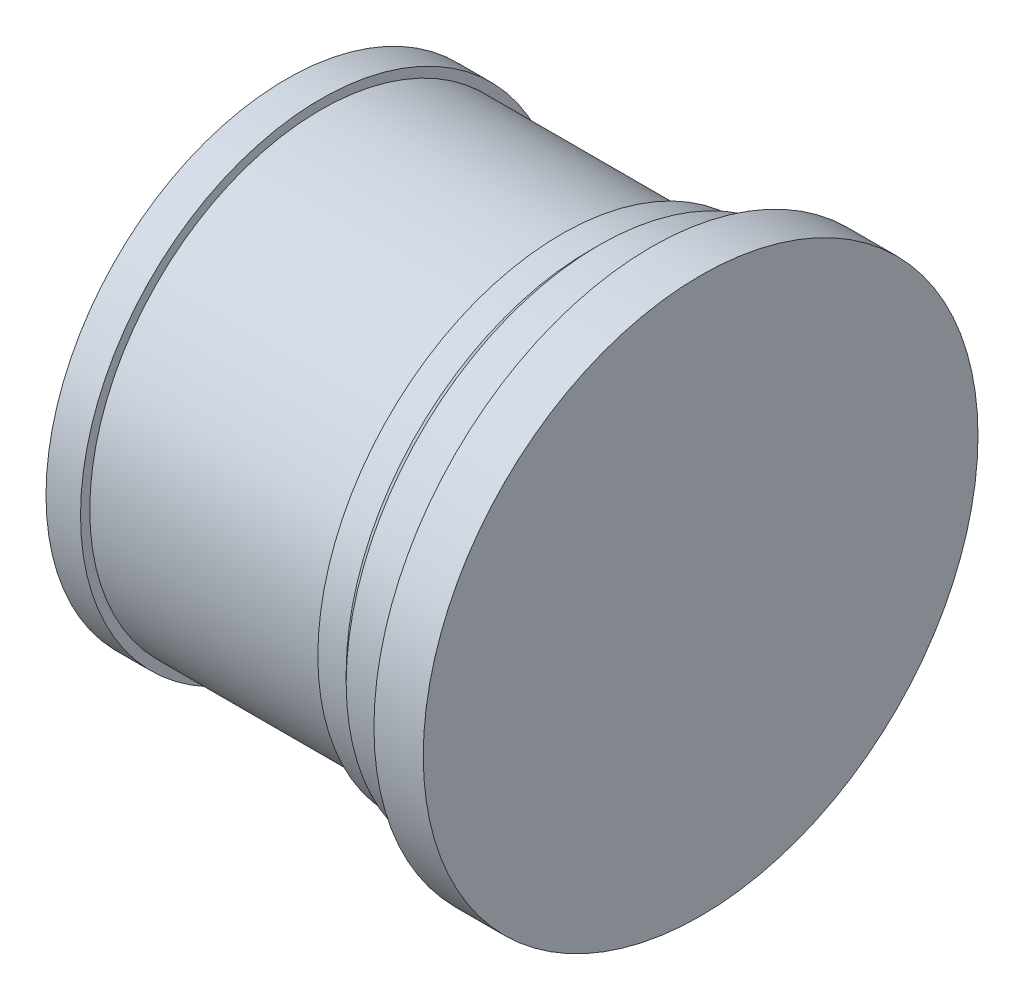
SolidWorks part; units mm, degrees
ref_plane "Front Plane" through (0, 0, 0) normal (0, 0, 1) x (1, 0, 0)
ref_plane "Top Plane" through (0, 0, 0) normal (0, 1, 0) x (1, 0, 0)
ref_plane "Right Plane" through (0, 0, 0) normal (1, 0, 0) x (0, 0, -1)
sketch "Sketch1" plane through (0, 0, 0) normal (0, 0, 1) x (1, 0, 0)
  line L0 (0, 0) -> (33.6, 0)
  line L1 (0, 0) -> (0, 19.5)
  line L2 (0, 19.5) -> (2.8, 19.5)
  line L3 (2.8, 19.5) -> (2.8, 18.75)
  line L4 (2.8, 18.75) -> (22.3, 18.75)
  line L5 (22.3, 18.75) -> (22.3, 19.75)
  line L6 (22.3, 19.75) -> (24.6, 19.75)
  line L7 (24.6, 19.75) -> (25.35, 20.5)
  line L8 (25.35, 20.5) -> (28.85, 20.5)
  line L9 (28.85, 20.5) -> (28.85, 19.75)
  line L10 (28.85, 19.75) -> (29.6, 19.75)
  line L11 (29.6, 19.75) -> (29.6, 22.5)
  line L12 (29.6, 22.5) -> (33.6, 22.5)
  line L13 (33.6, 22.5) -> (33.6, 0)
  point P3 (4.0408, 18.75)
  dimension "D1" = 33.6
  dimension "D2" = 20.5
  dimension "D3" = 22.5
  dimension "D4" = 4
  dimension "D5" = 5
  dimension "D6" = 0.75
  dimension "D7" = 0.75
  dimension "D8" = 0.75
  dimension "D9" = 0.75
  dimension "D10" = 2.3
  dimension "D11" = 18.75
  dimension "D12" = 19.5
  dimension "D13" = 19.5
revolve "Revolve1" add sketch "Sketch1" angle 360 about L0
